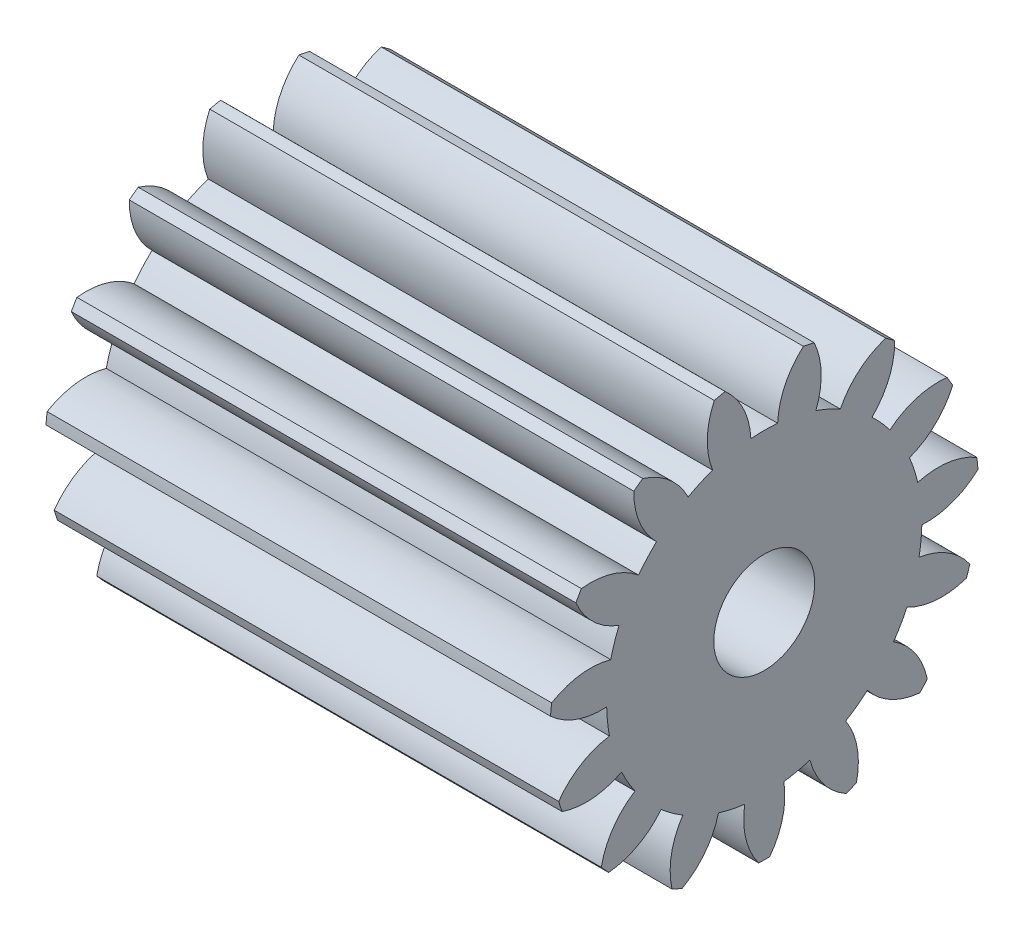
SolidWorks part; units mm, degrees
material "1.0035 (S185)"
ref_plane "Plane1" through (0, 0, 0) normal (0, 0, 1) x (1, 0, 0)
ref_plane "Plane2" through (0, 0, 0) normal (0, 1, 0) x (1, 0, 0)
ref_plane "Plane3" through (0, 0, 0) normal (1, 0, 0) x (0, 0, -1)
sketch "HoldingSke" plane through (0, 0, 0) normal (0, 1, 0) x (1, 0, 0)
  line L0 (0, 0) -> (1.9319, -0.5176)
  line L1 (-15, 0) -> (100, 0) construction
  line L2 (0, 0) -> (-2.1039, 2.3779)
  line L3 (0, 0) -> (-11.863, 4.5341)
  line L4 (0, 0) -> (8.3417, 2.2352)
  line L5 (0, 0) -> (-46.8476, -17.4728)
  line L6 (0, 0) -> (-8.2896, -5.593)
  line L7 (-2.1039, 2.3779) -> (8.6586, 51.2059)
  line L8 (-76.2, 54.61) -> (-75.9, 54.61)
  line L9 (-71.009, 38.7566) -> (-53.1078, 45.2721)
  line L10 (-76.2, 71.12) -> (104.1128, 71.12)
  line L11 (0, 0) -> (-10, 0)
  line L12 (-76.2, 101.6) -> (-76.181, 101.6)
  line L13 (24.9733, 27.94) -> (52.9518, 28.4284)
  line L14 (24.9733, 27.94) -> (24.9743, 27.94)
  line L15 (24.9733, 27.94) -> (100.4006, 29.5858)
  line L16 (-63.627, -0.5) -> (-12.827, -0.5)
  circle A0 centre (0, 0) radius 1
  circle A1 centre (0, 0) radius 3.124
  circle A2 centre (0, 0) radius 37.5
  circle A3 centre (0, 0) radius 1
  dimension "MHD" = 6.248
  dimension "Hub_dia" = 75
  dimension "Bore" = 2
  dimension "MBD" = 2
  dimension "Num_teeth" = 15
  dimension "Pitch_radius" = 180.3128
  dimension "Pitch" = 2
  dimension "Width" = 10
  dimension "Overall_len" = 50
  dimension "Show_teeth" = 15
  dimension "Thickness" = 10
  dimension "OAL" = 50.0001
  dimension "T_dim" = 0.3
  dimension "Ap" = 20
  dimension "H" = 19.05
  dimension "Backlash" = 0.019
  dimension "Addendum_fac" = 1
  dimension "Dedendum_fac" = 1.25
  dimension "Clearance_fac" = 0.25
  dimension "Dedendum_add" = 0.001
  dimension "Module" = 0.5
sketch "BasProSke" plane through (0, 0, 0) normal (0, 1, 0) x (1, 0, 0)
  line L0 (-10, 0) -> (60, 0) construction
  line L1 (0, 0) -> (0, 4.25)
  line L2 (0, 0) -> (10, 0)
  line L3 (10, 0) -> (10, 4.25)
  line L4 (10, 4.25) -> (0, 4.25)
  dimension "Diameter" = 8.5
  dimension "Thickness" = 10
revolve "Base-Revolve" add sketch "BasProSke" angle 360 about L0
sketch "TooCutSke" plane through (0, 0, 0) normal (1, 0, 0) x (0, 0, -1)
  line L1 (0, 0) -> (0, 107) construction
  line L2 (0, 0) -> (-0.4252, 3.7258) construction
  line L3 (0, 0) -> (-1.5522, 7.3025) construction
  line L4 (-0.4252, 3.7258) -> (-0.7761, 3.6512) construction
  arc A0 (0.2658, 3.1127) -> (-0.2658, 3.1127) centre (0, 0) ccw
  arc A1 (0.8008, 4.1997) -> (-0.8008, 4.1997) centre (0, 0) ccw
  circle A2 centre (0, 0) radius 3.75 construction
  circle A3 centre (0, 0) radius 3.5238 construction
  arc A4 (-0.2658, 3.1127) -> (-0.8008, 4.1997) centre (-1.7645, 3.0503) ccw
  arc A5 (0.8008, 4.1997) -> (0.2658, 3.1127) centre (1.7645, 3.0503) ccw
  dimension "Root_dia" = 6.248
  dimension "Overcut_dia" = 8.5508
  dimension "Pitch_dia" = 7.5
  dimension "Base_dia" = 7.0477
  dimension "Flank_rad" = 1.5
  dimension "Half_ang" = 12
  dimension "Half_CT" = 0.3587
extrude "ToothCut" cut sketch "TooCutSke" along normal through all
fillet "Breaks" [suppressed] radius 0.01
fillet "RootFillets" [suppressed] radius 0.126
pattern_circular "TeethCuts" count 15 every 24 about axis through (-10, 0, 0) along (1, 0, 0) of "ToothCut", "RootFillets", "Breaks"
sketch "HubNeaOneSke" plane through (0, 0, 0) normal (-1, 0, 0) x (0, 0, 1)
  circle A0 centre (0, 0) radius 3.124
  dimension "Diameter" = 6.248
extrude "HubNearOne" [suppressed] add sketch "HubNeaOneSke" along normal blind 40.0001
sketch "HubNeaBotSke" plane through (0, 0, 0) normal (-1, 0, 0) x (0, 0, 1)
  circle A0 centre (0, 0) radius 3.124
  dimension "Diameter" = 6.248
extrude "HubNearBoth" [suppressed] add sketch "HubNeaBotSke" along normal blind 20
ref_plane "FarPln" through (10, 0, 0) normal (1, 0, 0) x (0, 0, -1)
sketch "HubFarSke" plane through (10, 0, 0) normal (1, 0, 0) x (0, 0, -1)
  circle A0 centre (0, 0) radius 3.124
  dimension "Diameter" = 6.248
extrude "HubFar" [suppressed] add sketch "HubFarSke" along normal blind 20
sketch "BorSke" plane through (0, 0, 0) normal (1, 0, 0) x (0, 0, -1)
  circle A0 centre (0, 0) radius 1
  dimension "Diameter" = 2
extrude "Bore" cut sketch "BorSke" along normal mid plane 100.0001
sketch "KeySke" plane through (0, 0, 0) normal (1, 0, 0) x (0, 0, -1)
  line L0 (-0.4, 0) -> (-0.4, 1.3)
  line L1 (-0.4, 1.3) -> (0.4, 1.3)
  line L2 (0.4, 1.3) -> (0.4, 0)
  line L3 (0, 0) -> (0, 34) construction
  line L4 (-0.4, 0) -> (0.4, 0)
  dimension "Offset" = 1.3
  dimension "Width" = 0.8
extrude "Keyway" [suppressed] cut sketch "KeySke" along normal mid plane 100.0001
pattern_circular "Keyway2" [suppressed] count 2 every 90 about axis through (-10, 0, 0) along (1, 0, 0)
equation "' \"Module@HoldingSke\" = 6.35"
equation "' \"Num_teeth@HoldingSke\" = 12"
equation "' \"Ap@HoldingSke\" =  20"
equation "' \"Width@HoldingSke\" = 0.5 * 25.4"
equation "' \"Hub_dia@HoldingSke\"= 1 * 25.4"
equation "' \"Overall_len@HoldingSke\" = 1.0 * 25.4"
equation "' \"Bore@HoldingSke\" = 0.75 * 25.4"
equation "' \"T_dim@HoldingSke\" = 0.1 * 25.4"
equation "' \"Width@KeySke\" = 0.25 * 25.4"
equation "' \"Show_teeth@HoldingSke\" = 13"
equation "' \"Backlash@HoldingSke\" = 0.009 * 25.4"
equation "' \"Addendum_fac@HoldingSke\" = 1.0"
equation "' \"Dedendum_fac@HoldingSke\" = 1.25"
equation "' \"Dedendum_add@HoldingSke\" = 0.00005 * 25.4"
equation "' \"Clearance_fac@HoldingSke\" = 0.25"
equation "\"Pitch@HoldingSke\" = 1 / \"Module@HoldingSke\""
equation "\"Overcut_dia@TooCutSke\" = (\"Num_teeth@HoldingSke\" + 2 * \"Addendum_fac@HoldingSke\") / \"Pitch@HoldingSke\" + 0.002 * 25.4"
equation "\"Pitch_dia@TooCutSke\" = \"Num_teeth@HoldingSke\" / \"Pitch@HoldingSke\""
equation "\"Base_dia@TooCutSke\" = \"Num_teeth@HoldingSke\" / \"Pitch@HoldingSke\" * cos((\"Ap@HoldingSke\"  * 3.14159265 / 180))"
equation "\"Root_dia@TooCutSke\" = (\"Num_teeth@HoldingSke\" + 2) / \"Pitch@HoldingSke\" - 2 * (\"Addendum_fac@HoldingSke\" + \"Dedendum_fac@HoldingSke\") / \"Pitch@HoldingSke\" - \"Dedendum_add@HoldingSke\" * 2"
equation "\"Half_ang@TooCutSke\" = 180 / \"Num_teeth@HoldingSke\""
equation "\"Half_CT@TooCutSke\" = \"Num_teeth@HoldingSke\" / \"Pitch@HoldingSke\" * sin((3.14159265 / 2 / \"Num_teeth@HoldingSke\")) / 2 - 7 * \"Backlash@HoldingSke\" / 4"
equation "\"Flank_rad@TooCutSke\" = \"Num_teeth@HoldingSke\" / \"Pitch@HoldingSke\" / 5"
equation "\"Radius@RootFillets\" = \"Clearance_fac@HoldingSke\" / \"Pitch@HoldingSke\" + \"Dedendum_add@HoldingSke\""
equation "\"Break_rad@Breaks\" = 0.02 / \"Pitch@HoldingSke\""
equation "\"Thickness@HoldingSke\" = \"Width@HoldingSke\""
equation "\"OAL@HoldingSke\" = \"Thickness@HoldingSke\""
equation "\"MHD@HoldingSke\" = (\"Num_teeth@HoldingSke\" + 2) / \"Pitch@HoldingSke\" - 2 * (\"Addendum_fac@HoldingSke\" + \"Dedendum_fac@HoldingSke\")  / \"Pitch@HoldingSke\" - \"Dedendum_add@HoldingSke\" * 2"
equation "\"MBD@HoldingSke\" = (\"Num_teeth@HoldingSke\" + 2) / \"Pitch@HoldingSke\" - 2 * (\"Addendum_fac@HoldingSke\" + \"Dedendum_fac@HoldingSke\")  / \"Pitch@HoldingSke\" - \"Dedendum_add@HoldingSke\" * 2 - 0.002 * 25.4"
equation "\"MHD@HoldingSke\" = ((sgn( \"MHD@HoldingSke\" - \"Hub_dia@HoldingSke\" )-1)*( \"MHD@HoldingSke\" - \"Hub_dia@HoldingSke\" ))/-2+ \"Hub_dia@HoldingSke\""
equation "\"MBD@HoldingSke\" = ((sgn( \"MBD@HoldingSke\" - \"Bore@HoldingSke\" )-1)*( \"MBD@HoldingSke\" - \"Bore@HoldingSke\" ))/-2+ \"Bore@HoldingSke\""
equation "\"OAL@HoldingSke\" = ((sgn( \"OAL@HoldingSke\" - \"Overall_len@HoldingSke\" )+1)*( \"OAL@HoldingSke\" - \"Overall_len@HoldingSke\" ))/2 + \"Overall_len@HoldingSke\" + 0.000002 * 25.4"
equation "\"Num_teeth@TeethCuts\" = int( \"Show_teeth@HoldingSke\" ) + 1"
equation "\"Num_teeth@TeethCuts\" = ((sgn( \"Num_teeth@TeethCuts\" - \"Num_teeth@HoldingSke\" )-1)*( \"Num_teeth@TeethCuts\" - \"Num_teeth@HoldingSke\" ))/-2+ \"Num_teeth@HoldingSke\""
equation "\"Num_teeth@TeethCuts\" = ((sgn( \"Num_teeth@TeethCuts\" - 2.0)+1)*( \"Num_teeth@TeethCuts\" - 2.0))/2 +2.0"
equation "\"Angle@TeethCuts\" = 360.0 / \"Num_teeth@HoldingSke\""
equation "\"Diameter@BasProSke\" = (\"Num_teeth@HoldingSke\" + 2 * \"Addendum_fac@HoldingSke\") / \"Pitch@HoldingSke\""
equation "\"Thickness@BasProSke\"  = \"Thickness@HoldingSke\""
equation "' \"Fillet_rad@BasProSke\" =  \"Thickness@HoldingSke\" * 0.05"
equation "\"MHD@HoldingSke\" = ((sgn( \"MHD@HoldingSke\" - \"Root_dia@TooCutSke\" )-1)*( \"MHD@HoldingSke\" - \"Root_dia@TooCutSke\" ))/-2+ \"Root_dia@TooCutSke\""
equation "\"Diameter@HubNeaOneSke\" = \"MHD@HoldingSke\""
equation "\"Length@HubNearOne\" = \"OAL@HoldingSke\" - \"Thickness@BasProSke\""
equation "\"Diameter@HubNeaBotSke\" = \"MHD@HoldingSke\""
equation "\"Length@HubNearBoth\" = ( \"OAL@HoldingSke\" - \"Thickness@BasProSke\" ) / 2.0"
equation "\"Thickness@FarPln\" = \"Thickness@BasProSke\""
equation "\"Diameter@HubFarSke\" = \"MHD@HoldingSke\""
equation "\"Length@HubFar\" = ( \"OAL@HoldingSke\" - \"Thickness@BasProSke\" ) / 2.0"
equation "\"Diameter@BorSke\" = \"MBD@HoldingSke\""
equation "\"D1@Bore\" = \"OAL@HoldingSke\" * 2.0"
equation "\"D1@Keyway\" = \"OAL@HoldingSke\" * 2.0"
equation "\"Offset@KeySke\" = \"T_dim@HoldingSke\" + \"MBD@HoldingSke\" / 2.0"
